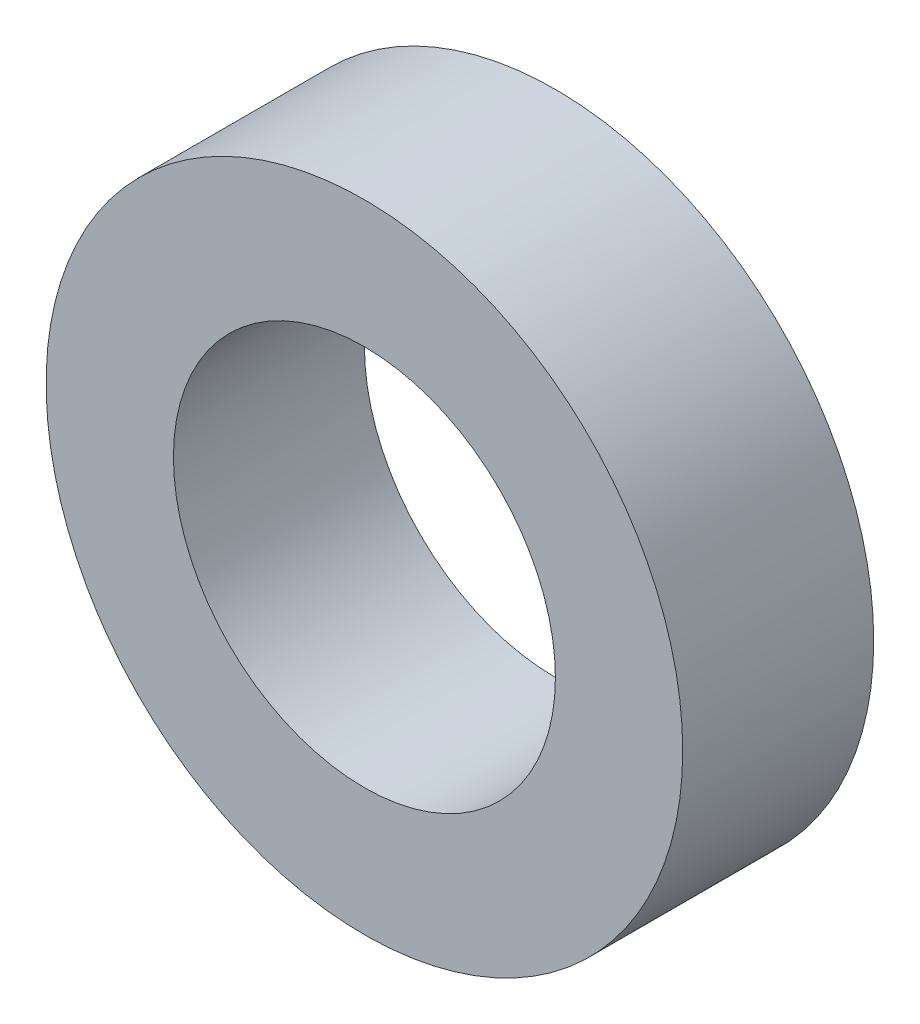
SolidWorks part; units mm, degrees
ref_plane "正面" through (0, 0, 0) normal (0, 0, 1) x (1, 0, 0)
ref_plane "平面" through (0, 0, 0) normal (0, 1, 0) x (1, 0, 0)
ref_plane "右側面" through (0, 0, 0) normal (1, 0, 0) x (0, 0, -1)
sketch "ｽｹｯﾁ1" plane through (0, 0, 0) normal (0, 0, 1) x (1, 0, 0)
  circle A0 centre (0, 0) radius 5
  circle A1 centre (0, 0) radius 3
  dimension "D1" = 10
  dimension "D2" = 6
extrude "ﾎﾞｽ - 押し出し1" add sketch "ｽｹｯﾁ1" along normal blind 3
